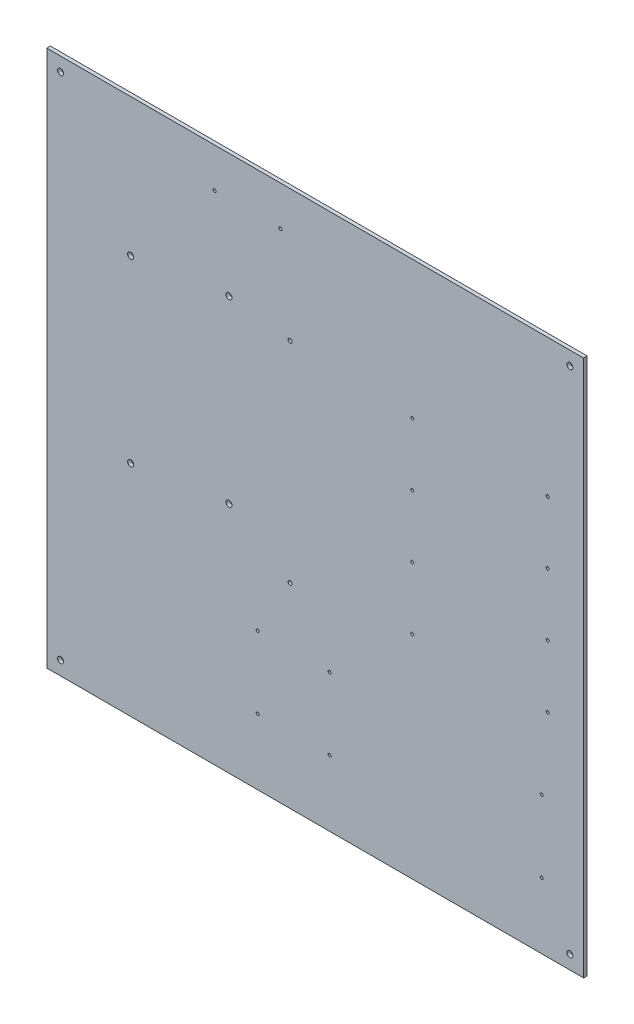
SolidWorks part; units mm, degrees
material "6061-T6 (SS)"
ref_plane "Piano frontale" through (0, 0, 0) normal (0, 0, 1) x (1, 0, 0)
ref_plane "Piano superiore" through (0, 0, 0) normal (0, 1, 0) x (1, 0, 0)
ref_plane "Piano destro" through (0, 0, 0) normal (1, 0, 0) x (0, 0, -1)
sketch "Schizzo1" plane through (0, 0, 0) normal (0, 0, 1) x (1, 0, 0)
  line L0 (0, 224) -> (448, 224) construction
  line L1 (0, 0) -> (448, 0)
  line L2 (0, 0) -> (0, 448)
  line L3 (0, 448) -> (448, 448)
  line L4 (448, 0) -> (448, 448)
  line L5 (224, 448) -> (224, 0) construction
  line L10 (0, 448) -> (0, 224) construction
  line L11 (0, 448) -> (0, 224) construction
  circle A0 centre (11.5, 436.5) radius 2.5
  circle A1 centre (436.5, 436.5) radius 2.5
  circle A2 centre (11.5, 11.5) radius 2.5
  circle A3 centre (436.5, 11.5) radius 2.5
  circle A4 centre (418, 177) radius 1.25
  circle A5 centre (305, 177) radius 1.25
  circle A6 centre (418, 229) radius 1.25
  circle A7 centre (305, 229) radius 1.25
  circle A8 centre (418, 281) radius 1.25
  circle A9 centre (305, 281) radius 1.25
  circle A10 centre (418, 333) radius 1.25
  circle A11 centre (305, 333) radius 1.25
  circle A12 centre (140, 415) radius 1.25
  circle A13 centre (195, 415) radius 1.25
  circle A14 centre (70, 333) radius 2.5
  circle A15 centre (70, 183) radius 2.5
  circle A16 centre (236, 55) radius 1.25
  circle A17 centre (236, 115) radius 1.25
  circle A18 centre (413, 115) radius 1.25
  circle A19 centre (413, 55) radius 1.25
  circle A20 centre (152, 344.7696) radius 2.5
  circle A21 centre (152, 194.7696) radius 2.5
  circle A22 centre (203, 338) radius 1.65
  circle A23 centre (203, 163) radius 1.65
  circle A24 centre (176, 115) radius 1.25
  circle A25 centre (176, 55) radius 1.25
  point P82 (253.9707, 256)
  point P89 (253.9707, 224)
  point P96 (253.9707, 192)
  point P103 (253.9707, 384)
  point P110 (253.9707, 352)
  point P117 (253.9707, 320)
  point P141 (253.9707, 288)
  point P148 (253.9707, 160)
  point P155 (253.9707, 128)
  point P162 (253.9707, 96)
  point P169 (253.9707, 64)
  point P179 (280.1758, 232.4048)
  point P193 (280.1085, 282.4047)
  point P207 (280.0413, 332.4047)
  dimension "D5" = 11.5
  dimension "D14" = 4
  dimension "D23" = 150
  dimension "D21" = 115
  dimension "D18" = 140
  dimension "D16" = 55
  dimension "D17" = 2.5
  dimension "D9" = 55
  dimension "D10" = 2.5
  dimension "D20" = 150
  dimension "D3" = 5
  dimension "D8" = 2.5
  dimension "D13" = 113
  dimension "D15" = 33
  dimension "D19" = 70
  dimension "D22" = 152
  dimension "D24" = 5
  dimension "D25" = 203
  dimension "D27" = 110
  dimension "D28" = 3.3
  dimension "D30" = 60
  dimension "D1" = 448
  dimension "D2" = 448
  dimension "D4" = 11.5
  dimension "D6" = 35
  dimension "D7" = 177
  dimension "D11" = 177
  dimension "D12" = 30
  dimension "D26" = 175
  dimension "D29" = 60
  dimension "D31" = 115
extrude "Estrusione-Estrusione1" add sketch "Schizzo1" against normal blind 3
